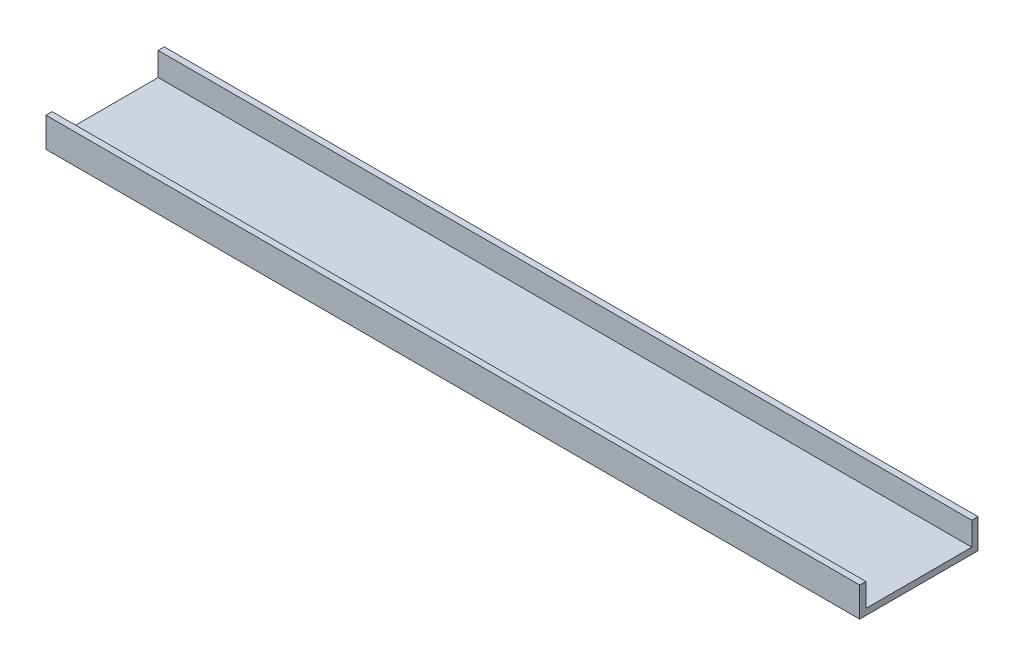
SolidWorks part; units mm, degrees
ref_plane "Front Plane" through (0, 0, 0) normal (0, 0, 1) x (1, 0, 0)
ref_plane "Top Plane" through (0, 0, 0) normal (0, 1, 0) x (1, 0, 0)
ref_plane "Right Plane" through (0, 0, 0) normal (1, 0, 0) x (0, 0, -1)
sketch "Sketch1" plane through (0, 0, 0) normal (0, 1, 0) x (1, 0, 0)
  line L1 (-165, 24) -> (165, 24)
  line L2 (-165, 24) -> (-165, -24)
  line L3 (-165, -24) -> (165, -24)
  line L4 (165, 24) -> (165, -24)
  point P4 (0, 24)
  point P6 (-165, 0)
  dimension "D1" = 330
  dimension "D2" = 48
extrude "Boss-Extrude1" add sketch "Sketch1" along normal blind 12
sketch "Sketch2" plane through (0, 0, 0) normal (1, 0, 0) x (0, 0, -1)
  line L0 (-24, 12) -> (24, 12) construction
  line L1 (-21.5, 12) -> (21.5, 12)
  line L2 (-21.5, 12) -> (-21.5, 2.5)
  line L3 (-21.5, 2.5) -> (21.5, 2.5)
  line L4 (21.5, 12) -> (21.5, 2.5)
  point P6 (0, 2.5)
  dimension "D1" = 43
  dimension "D2" = 9.5
extrude "Cut-Extrude1" cut sketch "Sketch2" against normal through all both and the other way through all
